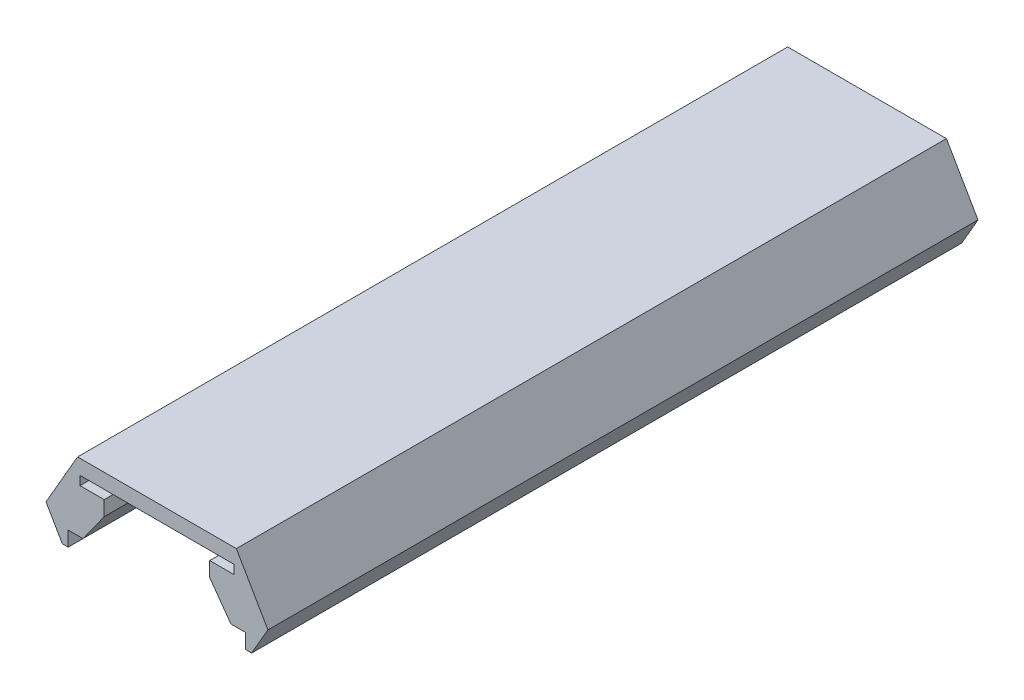
SolidWorks part; units mm, degrees
ref_plane "Front Plane" through (0, 0, 0) normal (0, 0, 1) x (1, 0, 0)
ref_plane "Top Plane" through (0, 0, 0) normal (0, 1, 0) x (1, 0, 0)
ref_plane "Right Plane" through (0, 0, 0) normal (1, 0, 0) x (0, 0, -1)
sketch "Sketch1" plane through (0, 0, 0) normal (0, 0, 1) x (1, 0, 0)
  line L0 (-5.2, 0) -> (5.2, 0)
  line L1 (-5.2, 0) -> (-5.2, -0.6)
  line L2 (-5.2, -0.6) -> (-3.5669, -0.6)
  line L3 (-3.5669, -0.6) -> (-3.5669, -1.6)
  line L4 (-3.5669, -1.6) -> (-5, -3.6)
  line L5 (-5, -3.6) -> (-6, -3.6)
  line L6 (-5.3668, 1) -> (5.3668, 1)
  line L7 (-5.3668, 1) -> (-7.5, -2.6947)
  line L8 (-7.5, -2.6947) -> (-6.4, -4.6)
  line L10 (-6, -4.6) -> (-6, -3.6)
  line L11 (0, -9.7207) -> (0, 9.7207) construction
  line L12 (6, -4.6) -> (6, -3.6)
  line L14 (7.5, -2.6947) -> (6.4, -4.6)
  line L15 (5.3668, 1) -> (7.5, -2.6947)
  line L16 (5, -3.6) -> (6, -3.6)
  line L17 (3.5669, -1.6) -> (5, -3.6)
  line L18 (3.5669, -0.6) -> (3.5669, -1.6)
  line L19 (5.2, -0.6) -> (3.5669, -0.6)
  line L20 (5.2, 0) -> (5.2, -0.6)
  line L21 (-6.4, -4.6) -> (-6, -4.6)
  line L22 (6, -4.6) -> (6.4, -4.6)
  point P3 (-7.5192, -2.8363)
  point P4 (0, 0)
  point P5 (-7.4925, -2.5624)
  point P18 (-7.5, -2.7539)
  point P19 (0, 0)
  point P25 (0, 1)
sketch "Sketch3" plane through (0, 0, 0) normal (0, 0, 1) x (1, 0, 0)
  line L5 (-7.5, -2.6947) -> (-6.4, -4.6) construction
  line L6 (7.5, -2.6947) -> (6.4, -4.6) construction
  line L7 (5.3668, 1) -> (7.5, -2.6947) construction
  line L8 (-5.3668, 1) -> (5.3668, 1) construction
  line L9 (-5.3668, 1) -> (-7.5, -2.6947) construction
  line L10 (7.7309, -2.6947) -> (6.5732, -4.7)
  line L11 (5.4823, 1.2) -> (7.7309, -2.6947)
  line L12 (-5.4823, 1.2) -> (5.4823, 1.2)
  line L13 (-5.4823, 1.2) -> (-7.7309, -2.6947)
  line L14 (-7.7309, -2.6947) -> (-6.5732, -4.7)
  line L15 (-6.5732, -4.7) -> (6.5732, -4.7)
  line L17 (0, -9.7207) -> (0, 9.7207) construction
  line L18 (-6.9, -10.9381) -> (6.9, -10.9381)
  line L19 (0, -10.9381) -> (0, -3.7) construction
  circle A0 centre (0, -3.7) radius 10 construction
  arc A1 (-6.9, -10.9381) -> (6.9, -10.9381) centre (0, -3.7) cw
  point P18 (0, -13.7)
sketch "Sketch2" plane through (0, 0, 0) normal (0, 0, 1) x (1, 0, 0)
  line L20 (7.5, -2.6947) -> (5.3668, 1)
  line L21 (6.4, -4.6) -> (7.5, -2.6947)
  line L22 (6, -4.6) -> (6.4, -4.6)
  line L23 (6, -3.6) -> (6, -4.6)
  line L24 (5, -3.6) -> (6, -3.6)
  line L25 (3.5669, -1.6) -> (5, -3.6)
  line L26 (3.5669, -0.6) -> (3.5669, -1.6)
  line L27 (5.2, -0.6) -> (3.5669, -0.6)
  line L28 (5.2, 0) -> (5.2, -0.6)
  line L29 (-5.2, 0) -> (5.2, 0)
  line L30 (-5.2, -0.6) -> (-5.2, 0)
  line L31 (-3.5669, -0.6) -> (-5.2, -0.6)
  line L32 (-3.5669, -1.6) -> (-3.5669, -0.6)
  line L33 (-5, -3.6) -> (-3.5669, -1.6)
  line L34 (-6, -3.6) -> (-5, -3.6)
  line L35 (-6, -4.6) -> (-6, -3.6)
  line L36 (-6.4, -4.6) -> (-6, -4.6)
  line L37 (-7.5, -2.6947) -> (-6.4, -4.6)
  line L38 (-5.3668, 1) -> (-7.5, -2.6947)
  line L39 (5.3668, 1) -> (-5.3668, 1)
  line L40 (7.5, -2.6947) -> (5.3668, 1)
  line L41 (6.4, -4.6) -> (7.5, -2.6947)
  line L42 (6, -4.6) -> (6.4, -4.6)
  line L43 (6, -3.6) -> (6, -4.6)
  line L44 (5, -3.6) -> (6, -3.6)
  line L45 (3.5669, -1.6) -> (5, -3.6)
  line L46 (3.5669, -0.6) -> (3.5669, -1.6)
  line L47 (5.2, -0.6) -> (3.5669, -0.6)
  line L48 (5.2, 0) -> (5.2, -0.6)
  line L49 (-5.2, 0) -> (5.2, 0)
  line L50 (-5.2, -0.6) -> (-5.2, 0)
  line L51 (-3.5669, -0.6) -> (-5.2, -0.6)
  line L52 (-3.5669, -1.6) -> (-3.5669, -0.6)
  line L53 (-5, -3.6) -> (-3.5669, -1.6)
  line L54 (-6, -3.6) -> (-5, -3.6)
  line L55 (-6, -4.6) -> (-6, -3.6)
  line L56 (-6.4, -4.6) -> (-6, -4.6)
  line L57 (-7.5, -2.6947) -> (-6.4, -4.6)
  line L58 (-5.3668, 1) -> (-7.5, -2.6947)
  line L59 (5.3668, 1) -> (-5.3668, 1)
  dimension "D1" = 0
extrude "Boss-Extrude1" add sketch "Sketch2" along normal mid plane 48
